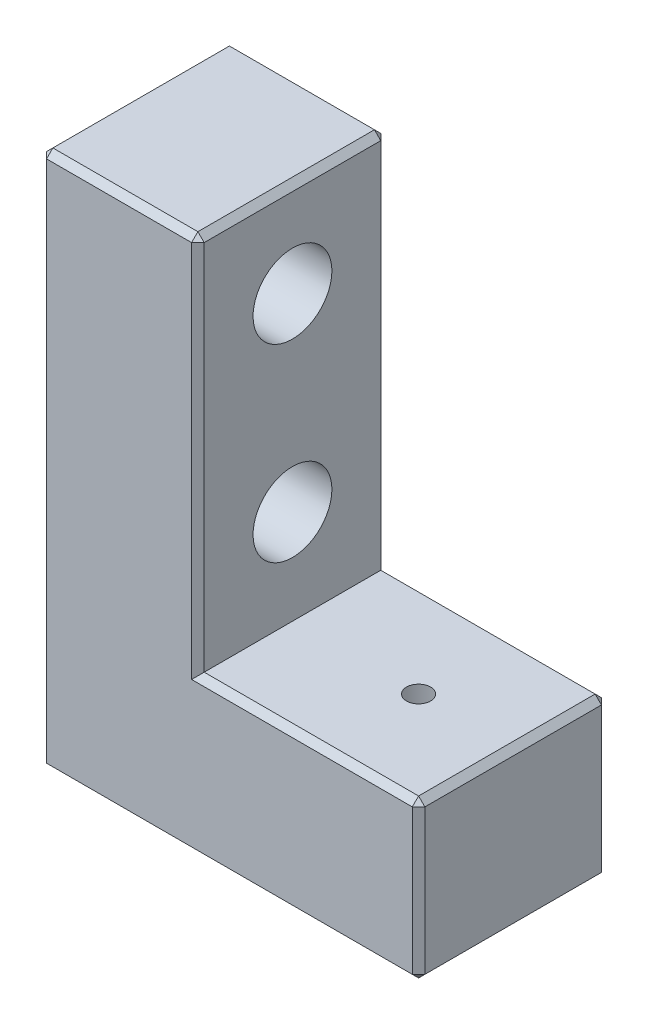
SolidWorks part; units mm, degrees
material "6061-T6 (SS)"
ref_plane "Front Plane" through (0, 0, 0) normal (0, 0, 1) x (1, 0, 0)
ref_plane "Top Plane" through (0, 0, 0) normal (0, 1, 0) x (1, 0, 0)
ref_plane "Right Plane" through (0, 0, 0) normal (1, 0, 0) x (0, 0, -1)
sketch "草图1" plane through (0, 0, 0) normal (0, 0, 1) x (1, 0, 0)
  line L0 (0, 17) -> (0, 0)
  line L1 (0, 0) -> (12, 0)
  line L2 (12, 0) -> (12, 5)
  line L3 (12, 5) -> (5, 5)
  line L4 (5, 5) -> (5, 17)
  line L5 (5, 17) -> (0, 17)
  dimension "D1" = 5
  dimension "D2" = 12
  dimension "D3" = 12
  dimension "D4" = 5
extrude "凸台-拉伸1" add sketch "草图1" along normal mid plane 6
sketch "草图2" plane through (5, 0, 0) normal (1, 0, 0) x (0, 0, -1)
  line L0 (-3, 17) -> (3, 17) construction
  circle A0 centre (0, 14) radius 1.25
  circle A1 centre (0, 8) radius 1.25
  dimension "D1" = 2.5
  dimension "D2" = 3
  dimension "D3" = 6
extrude "切除-拉伸1" cut sketch "草图2" against normal blind 6
cosmetic thread "孔螺蚊线1" parameters "D1"=3, "D2"=3
cosmetic thread "孔螺蚊线2" parameters "D1"=3, "D2"=3
cosmetic thread "孔螺蚊线5" parameters "D1"=4, "D2"=3
cosmetic thread "孔螺蚊线6" parameters "D1"=4, "D2"=3
sketch "草图3" plane through (0, 0, 0) normal (0, -1, 0) x (1, 0, 0)
  line L0 (0, 3) -> (0, -3) construction
  circle A0 centre (9, 0) radius 1.25
  circle A1 centre (3, 0) radius 1.25
  dimension "D1" = 3
  dimension "D2" = 2.5
  dimension "D3" = 6
extrude "切除-拉伸2" cut sketch "草图3" against normal blind 3
cosmetic thread "孔螺蚊线3" parameters "D1"=3, "D2"=3
cosmetic thread "孔螺蚊线4" parameters "D1"=3, "D2"=3
cosmetic thread "孔螺蚊线7" parameters "D1"=4, "D2"=3
cosmetic thread "孔螺蚊线8" parameters "D1"=4, "D2"=3
hole_wizard "M3 螺纹孔1" positions "3D草图1" profile "草图4" tap size "M3" standard "GB"
sketch3d "3D草图1"
  line L0 (3, 3, 0) -> (3, 0, 0) construction
  line L1 (9, 3, 0) -> (9, 0, 0) construction
  line L2 (0, 8, 0) -> (5, 8, 0) construction
  line L3 (0, 14, 0) -> (5, 14, 0) construction
  point P0 (3, 0, 0)
  point P4 (9, 0, 0)
  point P8 (0, 8, 0)
  point P12 (0, 14, 0)
sketch "草图4" plane through (3, 0, 0) normal (1, 0, 0) x (0, 0, -1)
  line L0 (0, 0) -> (0, 5.2217)
  line L1 (0, 5.2217) -> (1.25, 4.5)
  line L2 (1.25, 4.5) -> (1.25, 0)
  line L5 (1.25, 0) -> (0, 0)
  line L10 (0, 5.2217) -> (-1.25, 4.5) construction
  line L11 (0, -6.35) -> (0, 107.95) construction
  dimension "螺纹孔钻头直径" = 2.5
  dimension "螺纹孔钻头深度" = 4.5
  dimension "导头角度" = 120
chamfer "倒角1" distance 0.2 angle 45 16 edges at (5, 17, 0) (0, 17, 0) (12, 0, 0) (0, 8.5, -3) (6, 0, -3) (12, 2.5, -3) (2.5, 17, -3) (5, 11, -3) (8.5, 5, -3) (12, 5, 0) (5, 11, 3) (8.5, 5, 3) (12, 2.5, 3) (6, 0, 3) (0, 8.5, 3) (2.5, 17, 3)
chamfer "倒角2" distance 0.2 angle 45 1 edges at (0, 0, 0)
